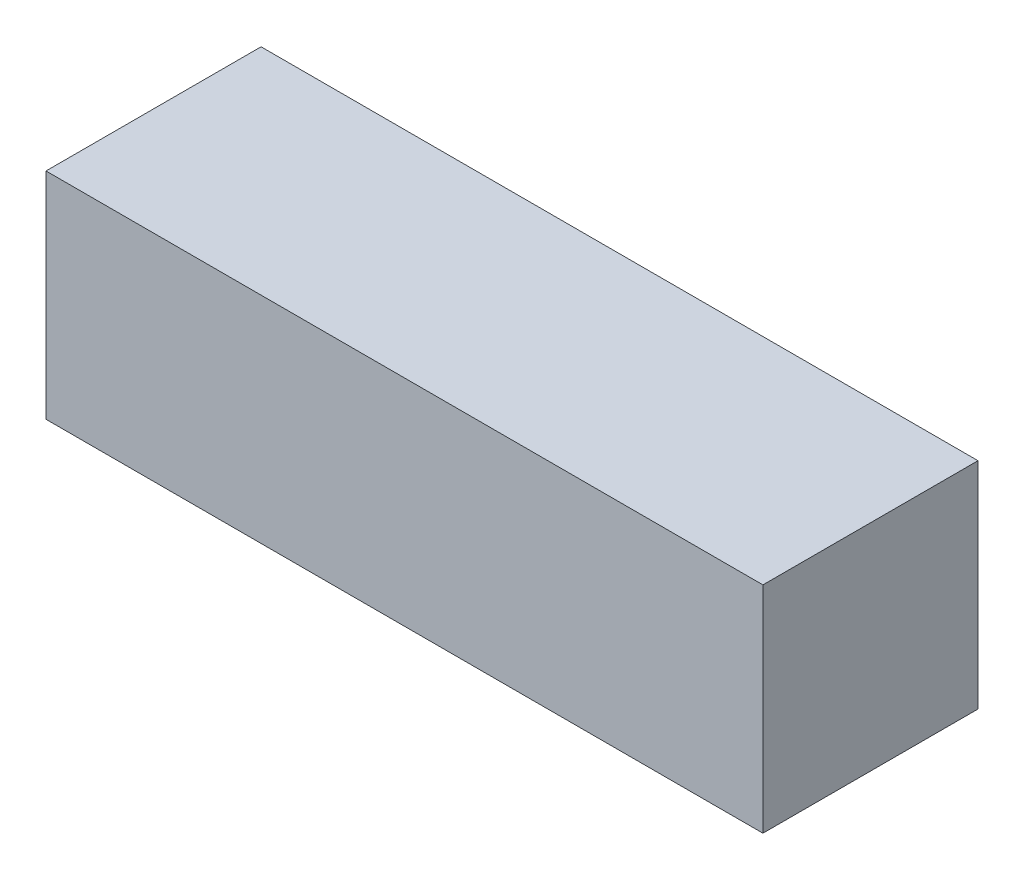
SolidWorks part; units mm, degrees
material "1023 Carbon Steel Sheet (SS)"
ref_plane "Front Plane" through (0, 0, 0) normal (0, 0, 1) x (1, 0, 0)
ref_plane "Top Plane" through (0, 0, 0) normal (0, 1, 0) x (1, 0, 0)
ref_plane "Right Plane" through (0, 0, 0) normal (1, 0, 0) x (0, 0, -1)
sketch "Sketch1" plane through (0, 0, 0) normal (0, 1, 0) x (1, 0, 0)
  line L1 (-100, -30) -> (100, -30)
  line L2 (-100, -30) -> (-100, 30)
  line L3 (-100, 30) -> (100, 30)
  line L4 (100, -30) -> (100, 30)
  line L5 (0, 30) -> (0, -30) construction
  line L6 (-100, 0) -> (100, 0) construction
  point P0 (0, 0)
  dimension "D1" = 200
  dimension "D2" = 60
extrude "Boss-Extrude1" add sketch "Sketch1" along normal blind 60
